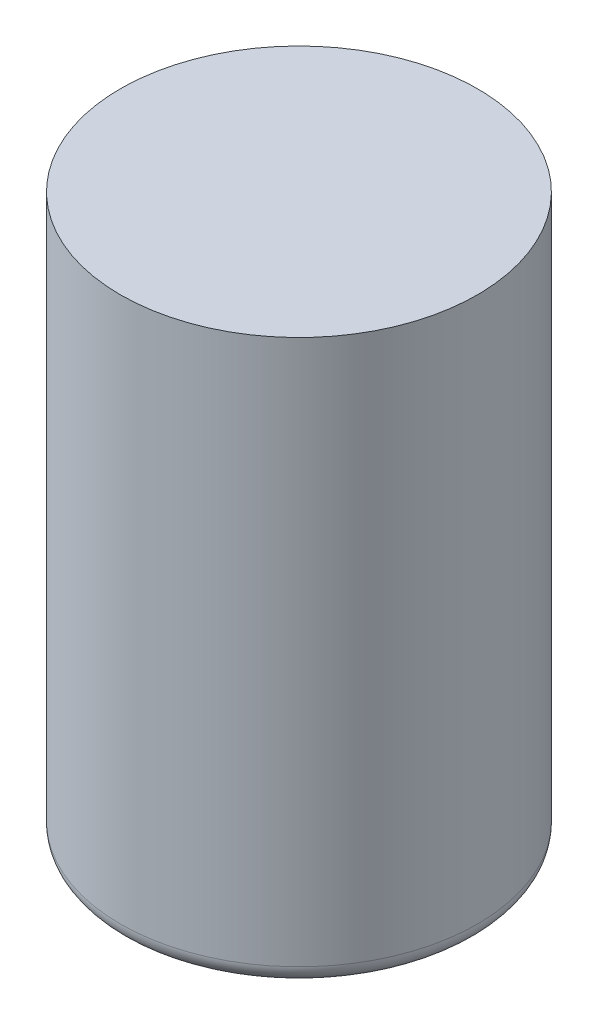
SolidWorks part; units mm, degrees
ref_plane "Front" through (0, 0, 0) normal (0, 0, 1) x (1, 0, 0)
ref_plane "Top" through (0, 0, 0) normal (0, 1, 0) x (1, 0, 0)
ref_plane "Right" through (0, 0, 0) normal (1, 0, 0) x (0, 0, -1)
sketch "Esquisse1" plane through (0, 0, 0) normal (0, 1, 0) x (1, 0, 0)
  circle A0 centre (0, 0) radius 9.5
  dimension "D1" = 19
extrude "Boss.-Extru.1" add sketch "Esquisse1" along normal blind 30
fillet "Congé1" radius 1 1 edges at (0, 0, 9.5)
scale "Echelle1" scale about origin uniform scaling yes scale factor 10
